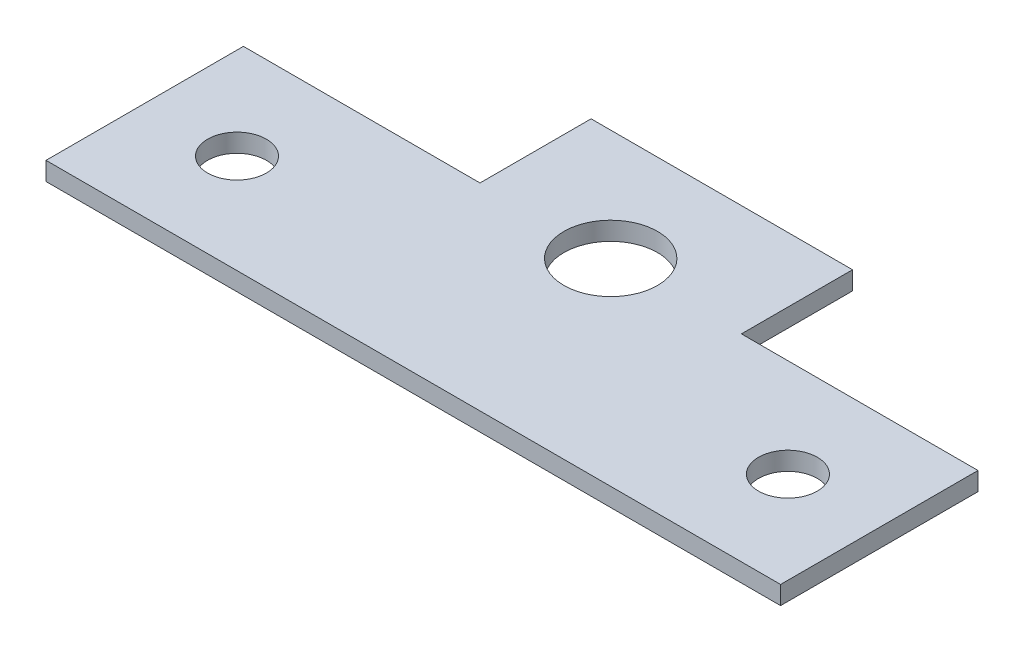
SolidWorks part; units mm, degrees
ref_plane "Спереди" through (0, 0, 0) normal (0, 0, 1) x (1, 0, 0)
ref_plane "Сверху" through (0, 0, 0) normal (0, 1, 0) x (1, 0, 0)
ref_plane "Справа" through (0, 0, 0) normal (1, 0, 0) x (0, 0, -1)
sketch "Эскиз1" plane through (0, 0, 0) normal (0, 1, 0) x (1, 0, 0)
  line L1 (-20, 8.4) -> (20, 8.4)
  line L2 (-20, 8.4) -> (-20, -8.4)
  line L3 (-20, -8.4) -> (20, -8.4)
  line L4 (20, 8.4) -> (20, -8.4)
  line L5 (-20, 8.4) -> (20, -8.4) construction
  line L6 (-20, -8.4) -> (20, 8.4) construction
  point P0 (0, 0)
extrude "Бобышка-Вытянуть1" add sketch "Эскиз1" along normal blind 1 contours L3 L4 L1 L2
sketch "Эскиз3" plane through (0, 1, 0) normal (0, 1, 0) x (1, 0, 0)
  line L0 (7.1175, 8.4) -> (7.1175, 2.35)
  line L1 (-20, 8.4) -> (-7.1175, 8.4)
  line L2 (-20, 8.4) -> (-20, 2.35)
  line L3 (-20, 2.35) -> (-7.1175, 2.35)
  line L4 (-7.1175, 8.4) -> (-7.1175, 2.35)
  line L5 (0, 11.6544) -> (0, -10.4612) construction
  line L6 (20, 2.35) -> (7.1175, 2.35)
  line L7 (20, 8.4) -> (20, 2.35)
  line L8 (20, 8.4) -> (7.1175, 8.4)
  circle A1 centre (-15, -3) radius 1.6
  circle A2 centre (15, -3) radius 1.6
  circle A3 centre (0, 2.35) radius 2.55
  point P13 (0, 0)
  point P14 (0, 0)
  point P18 (0, 0)
extrude "Вырез-Вытянуть1" cut sketch "Эскиз3" against normal through all
